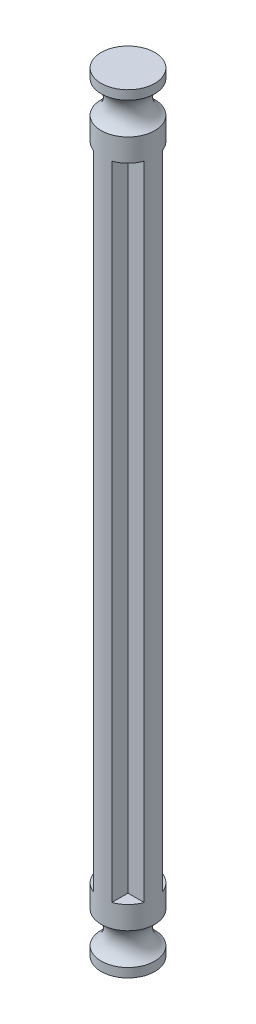
SolidWorks part; units mm, degrees
ref_plane "前视基准面" through (0, 0, 0) normal (0, 0, 1) x (1, 0, 0)
ref_plane "上视基准面" through (0, 0, 0) normal (0, 1, 0) x (1, 0, 0)
ref_plane "右视基准面" through (0, 0, 0) normal (1, 0, 0) x (0, 0, -1)
sketch "草图1" plane through (0, 0, 0) normal (0, 1, 0) x (1, 0, 0)
  line L0 (1, 1) -> (1, 2.7753)
  line L7 (1, 1) -> (2.7753, 1)
  line L8 (1, -1) -> (2.7753, -1)
  line L9 (1, -1) -> (1, -2.7753)
  line L10 (-1, -1) -> (-1, -2.7753)
  line L11 (-1, -1) -> (-2.7753, -1)
  line L12 (-1, 1) -> (-2.7753, 1)
  line L13 (-1, 1) -> (-1, 2.7753)
  arc A0 (-2.7753, 1) -> (-2.7753, -1) centre (0, 0) ccw
  arc A1 (-1, -2.7753) -> (1, -2.7753) centre (0, 0) ccw
  arc A2 (2.7753, -1) -> (2.7753, 1) centre (0, 0) ccw
  arc A3 (1, 2.7753) -> (-1, 2.7753) centre (0, 0) ccw
  dimension "D1" = 5.9
  dimension "D2" = 2
  dimension "D3" = 2
  dimension "D4" = 2
  dimension "D5" = 2
  dimension "D6" = 1
  dimension "D7" = 1
  dimension "D8" = 1
  dimension "D9" = 1
extrude "凸台-拉伸2" add sketch "草图1" along normal blind 70.64
sketch "草图3" plane through (0, 0, 0) normal (1, 0, 0) x (0, 0, -1)
  line L0 (0, 70.64) -> (0, 77.64)
  line L1 (1, 70.64) -> (-1, 70.64) construction
  line L2 (0, 77.64) -> (2.95, 77.64)
  line L3 (0, 70.64) -> (2.95, 70.64)
  line L4 (2.95, 70.64) -> (2.95, 73.14)
  line L5 (2.95, 77.64) -> (2.95, 76.64)
  line L6 (0, 0) -> (0, -7)
  line L7 (0, -7) -> (2.95, -7)
  line L8 (0, 0) -> (2.95, 0)
  line L9 (2.95, 0) -> (2.95, -2.5)
  line L10 (2.95, -7) -> (2.95, -6)
  arc A0 (2.95, 76.64) -> (2.95, 73.14) centre (3.9182, 74.89) ccw
  arc A1 (2.95, -2.5) -> (2.95, -6) centre (3.9182, -4.25) ccw
  dimension "D5" = 1
  dimension "D4" = 2
  dimension "D9" = 2
  dimension "D1" = 2.95
  dimension "D2" = 7
  dimension "D3" = 2.5
  dimension "D6" = 7
  dimension "D7" = 2.5
  dimension "D8" = 1
revolve "旋转3" add sketch "草图3" angle 360 about L6
